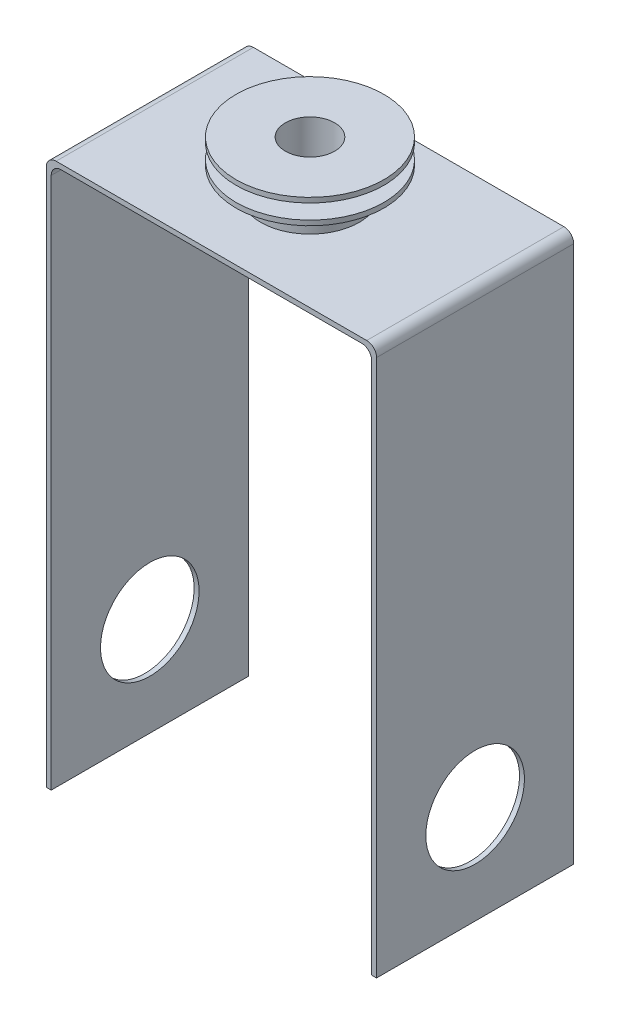
SolidWorks part; units mm, degrees
material "PE High Density"
ref_plane "Front Plane" through (0, 0, 0) normal (0, 0, 1) x (1, 0, 0)
ref_plane "Top Plane" through (0, 0, 0) normal (0, 1, 0) x (1, 0, 0)
ref_plane "Right Plane" through (0, 0, 0) normal (1, 0, 0) x (0, 0, -1)
sketch "Sketch1" plane through (0, 0, 0) normal (0, 0, 1) x (1, 0, 0)
  line L0 (42.545, 113.03) -> (42.545, -25.4)
  line L1 (-38.735, 114.3) -> (38.735, 114.3)
  line L2 (-41.275, 111.76) -> (-41.275, -25.4)
  line L4 (41.275, 111.76) -> (41.275, -25.4)
  line L5 (-41.275, 114.3) -> (41.275, -25.4) construction
  line L6 (-41.275, -25.4) -> (41.275, 114.3) construction
  line L7 (-40.005, 115.57) -> (40.005, 115.57)
  line L8 (-42.545, 113.03) -> (-42.545, -25.4)
  line L9 (-42.545, -25.4) -> (-41.275, -25.4)
  line L10 (41.275, -25.4) -> (42.545, -25.4)
  line L11 (41.275, 114.3) -> (41.275, -25.4) construction
  line L12 (-41.275, 114.3) -> (41.275, 114.3) construction
  line L13 (42.545, 115.57) -> (42.545, -25.4) construction
  line L14 (-42.545, 115.57) -> (42.545, 115.57) construction
  line L15 (-42.545, 115.57) -> (-42.545, -25.4) construction
  line L16 (-41.275, 114.3) -> (-41.275, -25.4) construction
  arc A0 (41.275, 111.76) -> (38.735, 114.3) centre (38.735, 111.76) ccw
  arc A1 (42.545, 113.03) -> (40.005, 115.57) centre (40.005, 113.03) ccw
  arc A2 (-42.545, 113.03) -> (-40.005, 115.57) centre (-40.005, 113.03) cw
  arc A3 (-41.275, 111.76) -> (-38.735, 114.3) centre (-38.735, 111.76) cw
  point P0 (0, 44.45)
  dimension "D6" = 2.54
  dimension "D1" = 82.55
  dimension "D2" = 1.27
  dimension "D3" = 139.7
  dimension "D4" = 82.55
  dimension "D5" = 114.3
extrude "Boss-Extrude1" add sketch "Sketch1" along normal blind 50.8 contours L8 L9 L2 A3 L1 A0 L4 L10 L0 A1 L7 A2
sketch "Sketch2" plane through (-42.545, 0, 0) normal (-1, 0, 0) x (0, 0, 1)
  line L1 (50.8, -25.4) -> (0, -25.4) construction
  circle A0 centre (25.4, 0) radius 12.7
  point P6 (25.4, -25.4)
  dimension "D1" = 25.4
  dimension "D2" = 25.4
extrude "Cut-Extrude1" cut sketch "Sketch2" against normal through all
sketch "Sketch3" plane through (0, 115.57, 0) normal (0, 1, 0) x (1, 0, 0)
  line L0 (-42.545, -50.8) -> (-42.545, 0) construction
  circle A0 centre (0, -25.4) radius 12.7
  point P4 (-42.545, -25.4)
  dimension "D1" = 25.4
extrude "Boss-Extrude2" add sketch "Sketch3" along normal blind 6.35 contours A0
sketch "Sketch4" plane through (0, 121.92, 0) normal (0, 1, 0) x (1, 0, 0)
  line L0 (-40.005, 0) -> (40.005, 0) construction
  circle A0 centre (0, -25.4) radius 19.05
  point P2 (0, 0)
  point P4 (0, 0)
  dimension "D1" = 38.1
  dimension "D2" = 25.4
extrude "Boss-Extrude3" add sketch "Sketch4" along normal blind 1.27
sketch "Sketch5" plane through (0, 123.19, 0) normal (0, 1, 0) x (1, 0, 0)
  circle A0 centre (0, -25.4) radius 6.35
  dimension "D1" = 12.7
extrude "Cut-Extrude2" cut sketch "Sketch5" against normal up to next
sketch "Sketch6" plane through (0, 123.19, 0) normal (0, 1, 0) x (1, 0, 0)
  circle A0 centre (0, -25.4) radius 12.7
  dimension "D1" = 25.4
extrude "Boss-Extrude4" add sketch "Sketch6" along normal blind 3.81
sketch "Sketch7" plane through (0, 127, 0) normal (0, 1, 0) x (1, 0, 0)
  circle A0 centre (0, -25.4) radius 19.05
  dimension "D1" = 38.1
extrude "Boss-Extrude5" add sketch "Sketch7" along normal blind 1.27 contours A0
hole_wizard "1/16 (0.5) Diameter Hole1" positions "Sketch8" profile "Sketch9" hole size "1/16" standard "ANSI Inch" end condition through all
sketch "Sketch8" plane through (0, 128.27, 0) normal (0, 1, 0) x (1, 0, 0)
  point P0 (0, -25.4)
sketch "Sketch9" plane through (0, 128.27, 25.4) normal (1, 0, 0) x (0, 0, 1)
  line L0 (0, 0) -> (0, 153.67)
  line L1 (0, 153.67) -> (6.35, 153.67)
  line L2 (6.35, 153.67) -> (6.35, 0)
  line L5 (6.35, 0) -> (0, 0)
  line L11 (0, -6.35) -> (0, 107.95) construction
  dimension "Thru Hole Dia." = 12.7
  dimension "Thru Hole Depth" = 153.67
